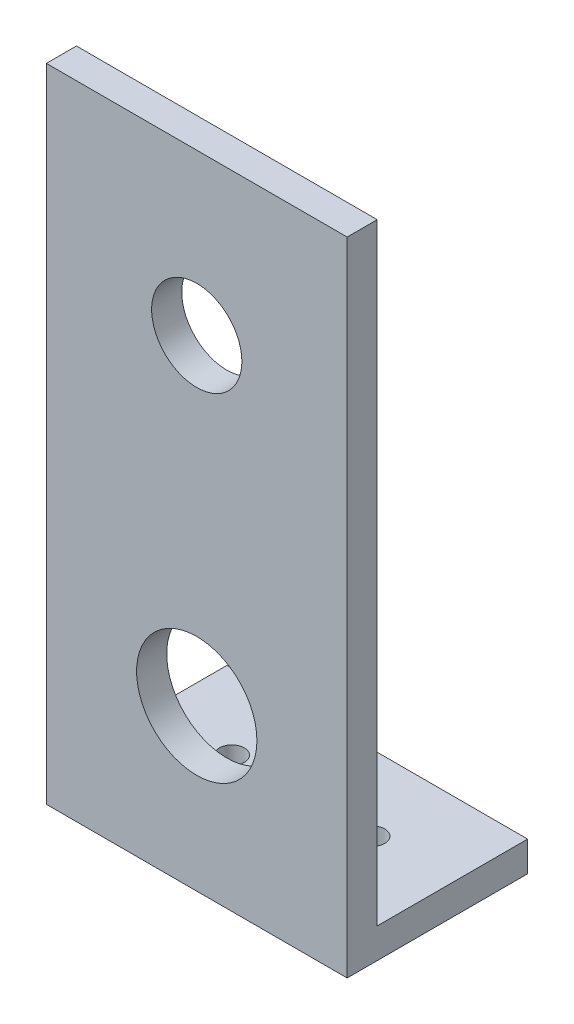
SolidWorks part; units mm, degrees
ref_plane "Front Plane" through (0, 0, 0) normal (0, 0, 1) x (1, 0, 0)
ref_plane "Top Plane" through (0, 0, 0) normal (0, 1, 0) x (1, 0, 0)
ref_plane "Right Plane" through (0, 0, 0) normal (1, 0, 0) x (0, 0, -1)
sketch "Sketch1" plane through (0, 0, 0) normal (0, 0, 1) x (1, 0, 0)
  line L1 (-31.8014, -25.7814) -> (-1.8014, -25.7814)
  line L2 (-31.8014, -25.7814) -> (-31.8014, 38.2186)
  line L3 (-31.8014, 38.2186) -> (-1.8014, 38.2186)
  line L4 (-1.8014, -25.7814) -> (-1.8014, 38.2186)
  dimension "D1" = 64
  dimension "D2" = 30
extrude "Boss-Extrude1" add sketch "Sketch1" along normal blind 3
sketch "Sketch2" plane through (0, 0, 3) normal (0, 0, 1) x (1, 0, 0)
  line L0 (-31.8014, -25.7814) -> (-1.8014, -25.7814) construction
  line L1 (-1.8014, 38.2186) -> (-31.8014, 38.2186) construction
  line L2 (-31.8014, 38.2186) -> (-31.8014, -25.7814) construction
  circle A0 centre (-16.8014, 22.2186) radius 4.5
  circle A1 centre (-16.8014, -9.7814) radius 6
  point P4 (-16.8014, -25.7814)
  point P7 (-16.8014, -25.7814)
  dimension "D1" = 16
  dimension "D2" = 0
  dimension "D3" = 16
  dimension "D4" = 15
extrude "Cut-Extrude1" cut sketch "Sketch2" against normal blind 3
sketch "Sketch4" plane through (0, 0, 0) normal (0, 0, -1) x (-1, 0, 0)
  line L0 (31.8014, 38.2186) -> (31.8014, -25.7814) construction
  line L1 (1.8014, -25.7814) -> (31.8014, -25.7814)
  line L2 (1.8014, -25.7814) -> (1.8014, -22.7814)
  line L3 (1.8014, -22.7814) -> (31.8014, -22.7814)
  line L4 (31.8014, -25.7814) -> (31.8014, -22.7814)
  dimension "D1" = 3
extrude "Boss-Extrude3" add sketch "Sketch4" along normal blind 15
sketch "Sketch5" plane through (0, -22.7814, 0) normal (0, 1, 0) x (1, 0, 0)
  line L0 (-1.8014, 15) -> (-1.8014, 0) construction
  line L1 (-31.8014, 15) -> (-31.8014, 0) construction
  circle A0 centre (-9.8014, 7.5) radius 1.25
  circle A1 centre (-23.8014, 7.5) radius 1.25
  dimension "D1" = 8
  dimension "D2" = 8
extrude "Cut-Extrude2" cut sketch "Sketch5" against normal blind 15
